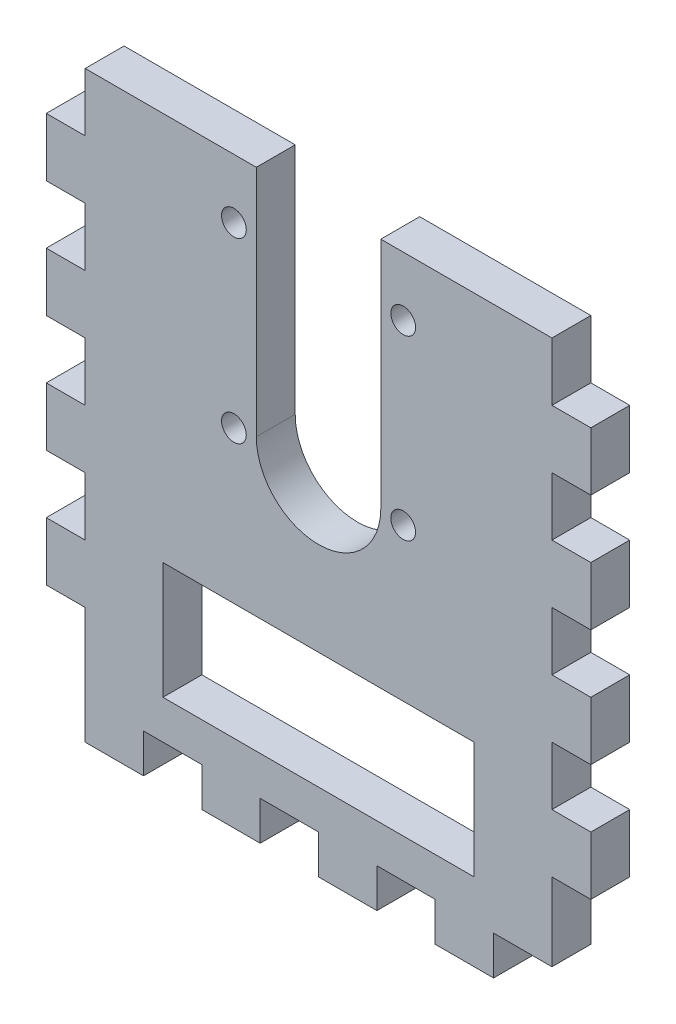
SolidWorks part; units mm, degrees
material "Pine"
ref_plane "Front Plane" through (0, 0, 0) normal (0, 0, 1) x (1, 0, 0)
ref_plane "Top Plane" through (0, 0, 0) normal (0, 1, 0) x (1, 0, 0)
ref_plane "Right Plane" through (0, 0, 0) normal (1, 0, 0) x (0, 0, -1)
sketch "Sketch1" plane through (0, 0, 0) normal (0, 0, 1) x (1, 0, 0)
  line L1 (0, 0) -> (76.2, 0)
  line L2 (0, 0) -> (0, -88.9)
  line L3 (0, -88.9) -> (76.2, -88.9)
  line L4 (76.2, 0) -> (76.2, -88.9)
  dimension "D1" = 88.9
  dimension "D2" = 76.2
extrude "Boss-Extrude1" add sketch "Sketch1" along normal blind 6.35
sketch "Sketch2" plane through (0, 0, 6.35) normal (0, 0, 1) x (1, 0, 0)
  line L0 (38.1, 0) -> (38.1, -38.1) construction
  line L1 (48.26, 0) -> (48.26, -38.1)
  line L2 (27.94, 0) -> (27.94, -38.1)
  line L3 (0, -88.9) -> (76.2, -88.9) construction
  line L4 (76.2, 0) -> (0, 0) construction
  line L5 (12.7, -63.5) -> (63.5, -63.5)
  line L6 (12.7, -63.5) -> (12.7, -82.55)
  line L7 (12.7, -82.55) -> (63.5, -82.55)
  line L8 (63.5, -63.5) -> (63.5, -82.55)
  line L9 (0, 0) -> (0, -88.9) construction
  arc A0 (48.26, 0) -> (27.94, 0) centre (38.1, 0) ccw
  arc A1 (27.94, -38.1) -> (48.26, -38.1) centre (38.1, -38.1) ccw
  circle A2 centre (51.9176, -9.652) radius 2.0193
  circle A3 centre (51.9176, -38.608) radius 2.0193
  circle A4 centre (24.2824, -38.6842) radius 2.0193
  circle A5 centre (24.2824, -9.652) radius 2.0193
  point P2 (38.1, -19.05)
  point P7 (38.1, -48.26)
  dimension "D2" = 10.16
  dimension "D3" = 4.0386
  dimension "D5" = 9.652
  dimension "D6" = 13.8176
  dimension "D7" = 13.8176
  dimension "D8" = 9.652
  dimension "D9" = 28.956
  dimension "D10" = 4.0386
  dimension "D11" = 4.0386
  dimension "D12" = 4.0386
  dimension "D1" = 48.26
  dimension "D4" = 29.0322
  dimension "D13" = 50.8
  dimension "D14" = 19.05
  dimension "D15" = 6.35
  dimension "D16" = 12.7
extrude "Cut-Extrude1" cut sketch "Sketch2" against normal up to surface (6.35 mm away) up to face at (38.1, -44.45, 0)
sketch "Sketch3" plane through (0, 0, 0) normal (0, 0, 1) x (1, 0, 0)
  line L1 (0, -9.525) -> (-6.35, -9.525)
  line L2 (0, -9.525) -> (0, -19.05)
  line L3 (0, -19.05) -> (-6.35, -19.05)
  line L4 (-6.35, -9.525) -> (-6.35, -19.05)
  line L5 (76.2, -88.9) -> (76.2, 0) construction
  line L6 (0, -28.575) -> (0, -38.1)
  line L7 (0, -28.575) -> (-6.35, -28.575)
  line L8 (-6.35, -28.575) -> (-6.35, -38.1)
  line L9 (0, -38.1) -> (-6.35, -38.1)
  line L10 (0, -47.625) -> (0, -57.15)
  line L11 (0, -47.625) -> (-6.35, -47.625)
  line L12 (-6.35, -47.625) -> (-6.35, -57.15)
  line L13 (0, -57.15) -> (-6.35, -57.15)
  line L14 (0, -66.675) -> (0, -76.2)
  line L15 (0, -66.675) -> (-6.35, -66.675)
  line L16 (-6.35, -66.675) -> (-6.35, -76.2)
  line L17 (0, -76.2) -> (-6.35, -76.2)
  line L23 (0, -88.9) -> (9.525, -88.9)
  line L24 (0, -88.9) -> (0, -95.25)
  line L25 (0, -95.25) -> (9.525, -95.25)
  line L26 (9.525, -88.9) -> (9.525, -95.25)
  line L27 (19.05, -88.9) -> (19.05, -95.25)
  line L28 (19.05, -88.9) -> (28.575, -88.9)
  line L29 (28.575, -88.9) -> (28.575, -95.25)
  line L30 (19.05, -95.25) -> (28.575, -95.25)
  line L31 (38.1, -88.9) -> (38.1, -95.25)
  line L32 (38.1, -88.9) -> (47.625, -88.9)
  line L33 (47.625, -88.9) -> (47.625, -95.25)
  line L34 (38.1, -95.25) -> (47.625, -95.25)
  line L35 (57.15, -88.9) -> (57.15, -95.25)
  line L36 (57.15, -88.9) -> (66.675, -88.9)
  line L37 (66.675, -88.9) -> (66.675, -95.25)
  line L38 (57.15, -95.25) -> (66.675, -95.25)
  line L39 (38.1, 0) -> (38.1, -88.9) construction
  line L40 (76.2, -66.675) -> (82.55, -66.675)
  line L41 (82.55, -66.675) -> (82.55, -76.2)
  line L42 (76.2, -76.2) -> (82.55, -76.2)
  line L43 (76.2, -66.675) -> (76.2, -76.2)
  line L44 (76.2, -47.625) -> (82.55, -47.625)
  line L45 (82.55, -47.625) -> (82.55, -57.15)
  line L46 (76.2, -57.15) -> (82.55, -57.15)
  line L47 (76.2, -47.625) -> (76.2, -57.15)
  line L48 (76.2, -28.575) -> (82.55, -28.575)
  line L49 (82.55, -28.575) -> (82.55, -38.1)
  line L50 (76.2, -38.1) -> (82.55, -38.1)
  line L51 (76.2, -28.575) -> (76.2, -38.1)
  line L52 (76.2, -19.05) -> (82.55, -19.05)
  line L53 (82.55, -9.525) -> (82.55, -19.05)
  line L54 (76.2, -9.525) -> (82.55, -9.525)
  line L55 (76.2, -9.525) -> (76.2, -19.05)
  line L56 (0, 0) -> (0, -88.9) construction
  line L57 (27.94, 0) -> (0, 0) construction
  line L58 (0, -88.9) -> (76.2, -88.9) construction
  dimension "D1" = 6.35
  dimension "D2" = 9.525
  dimension "D3" = 9.525
  dimension "D5" = 9.525
  dimension "D6" = 6.35
  dimension "D8" = 9.525
  dimension "D9" = 4
  dimension "D10" = 9.525
  dimension "D4" = 4
extrude "Boss-Extrude3" add sketch "Sketch3" along normal up to surface (6.35 mm away) up to face at (22.2631, -38.6842, 6.35)
